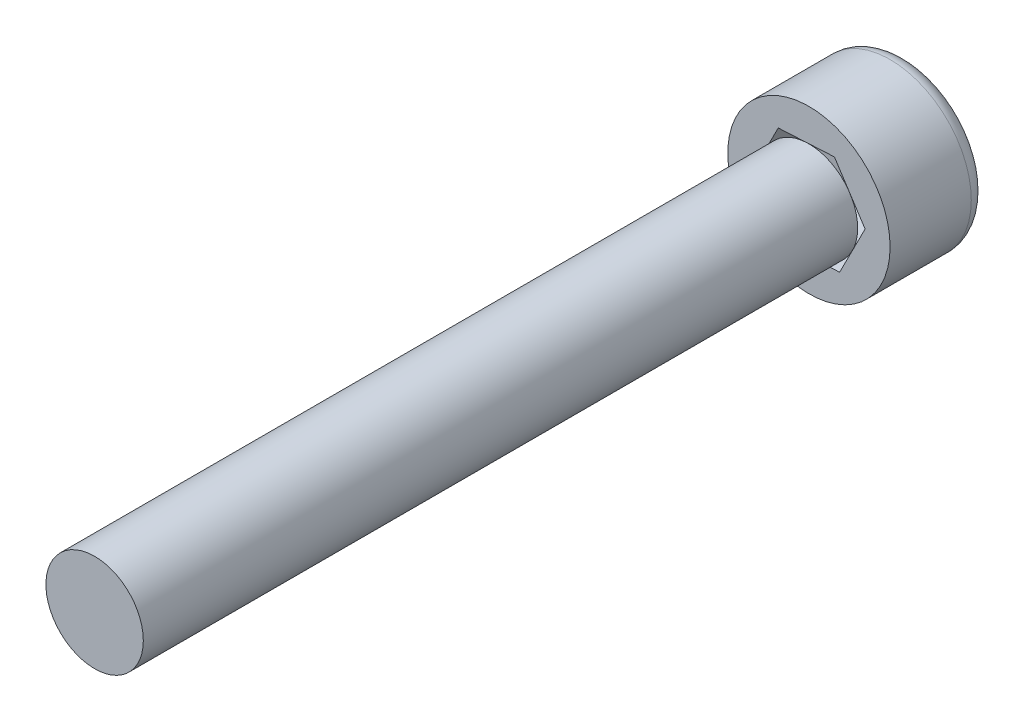
SolidWorks part; units mm, degrees
ref_plane "Front Plane" through (0, 0, 0) normal (0, 0, 1) x (1, 0, 0)
ref_plane "Top Plane" through (0, 0, 0) normal (0, 1, 0) x (1, 0, 0)
ref_plane "Right Plane" through (0, 0, 0) normal (1, 0, 0) x (0, 0, -1)
sketch "Sketch1" plane through (0, 0, 0) normal (0, 0, 1) x (1, 0, 0)
  circle A0 centre (0, 0) radius 2.5
  dimension "D1" = 5
extrude "Boss-Extrude1" add sketch "Sketch1" along normal blind 3
sketch "Sketch2" plane through (0, 0, 3) normal (0, 0, 1) x (1, 0, 0)
  circle A0 centre (0, 0) radius 1.5
  dimension "D1" = 3
extrude "Boss-Extrude2" add sketch "Sketch2" along normal blind 22
sketch "Sketch3" plane through (0, 0, 0) normal (0, 0, -1) x (-1, 0, 0)
  line L1 (0.7845, -1.5442) -> (1.7296, -0.0927)
  line L2 (1.7296, -0.0927) -> (0.9451, 1.4515)
  line L3 (0.9451, 1.4515) -> (-0.7845, 1.5442)
  line L4 (-0.7845, 1.5442) -> (-1.7296, 0.0927)
  line L5 (-1.7296, 0.0927) -> (-0.9451, -1.4515)
  line L6 (-0.9451, -1.4515) -> (0.7845, -1.5442)
  circle A0 centre (0, 0) radius 1.5 construction
  dimension "D1" = 3
extrude "Cut-Extrude1" cut sketch "Sketch3" against normal blind 3
fillet "Fillet1" radius 0.5 1 edges at (2.5, 0, 0)
